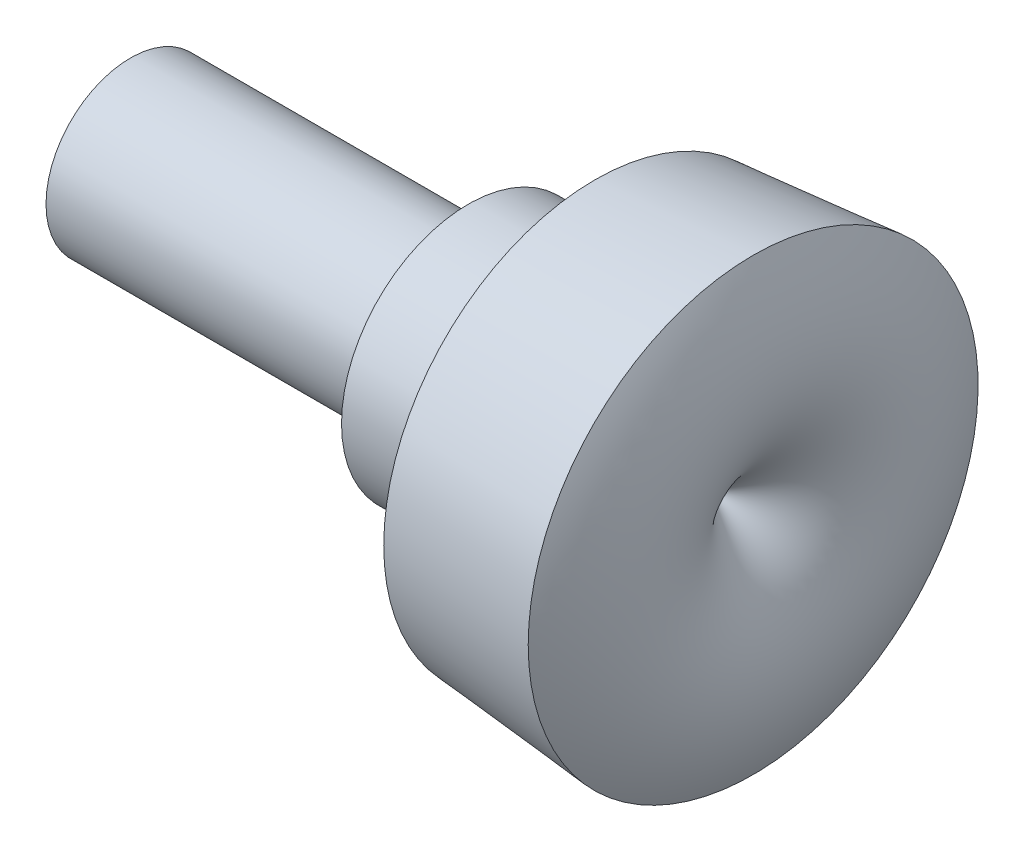
SolidWorks part; units mm, degrees
material "Stainless Steel (ferritic)"
ref_plane "Front Plane" through (0, 0, 0) normal (0, 0, 1) x (1, 0, 0)
ref_plane "Top Plane" through (0, 0, 0) normal (0, 1, 0) x (1, 0, 0)
ref_plane "Right Plane" through (0, 0, 0) normal (1, 0, 0) x (0, 0, -1)
sketch "Sketch2" plane through (0, 0, 0) normal (0, 0, 1) x (1, 0, 0)
  line L0 (0, 0) -> (0, 2)
  line L1 (0, 2) -> (8, 2)
  line L2 (8, 2) -> (8, 3)
  line L3 (8, 3) -> (11, 3)
  line L4 (11, 3) -> (11, 5)
  line L5 (11, 5) -> (14.75, 5.3281)
  line L6 (0, 0) -> (13.75, 0)
  spline S0 degree 2 poles (14.75, 5.3281) (16.4784, 2.1012) (13.75, 0) knots 0 0 0 1 1 1
  dimension "D1" = 2
  dimension "D2" = 8
  dimension "D3" = 1
  dimension "D4" = 3
  dimension "D5" = 2
  dimension "D6" = 95
  dimension "D7" = 3.75
revolve "Revolve1" add sketch "Sketch2" angle 360 about L6
